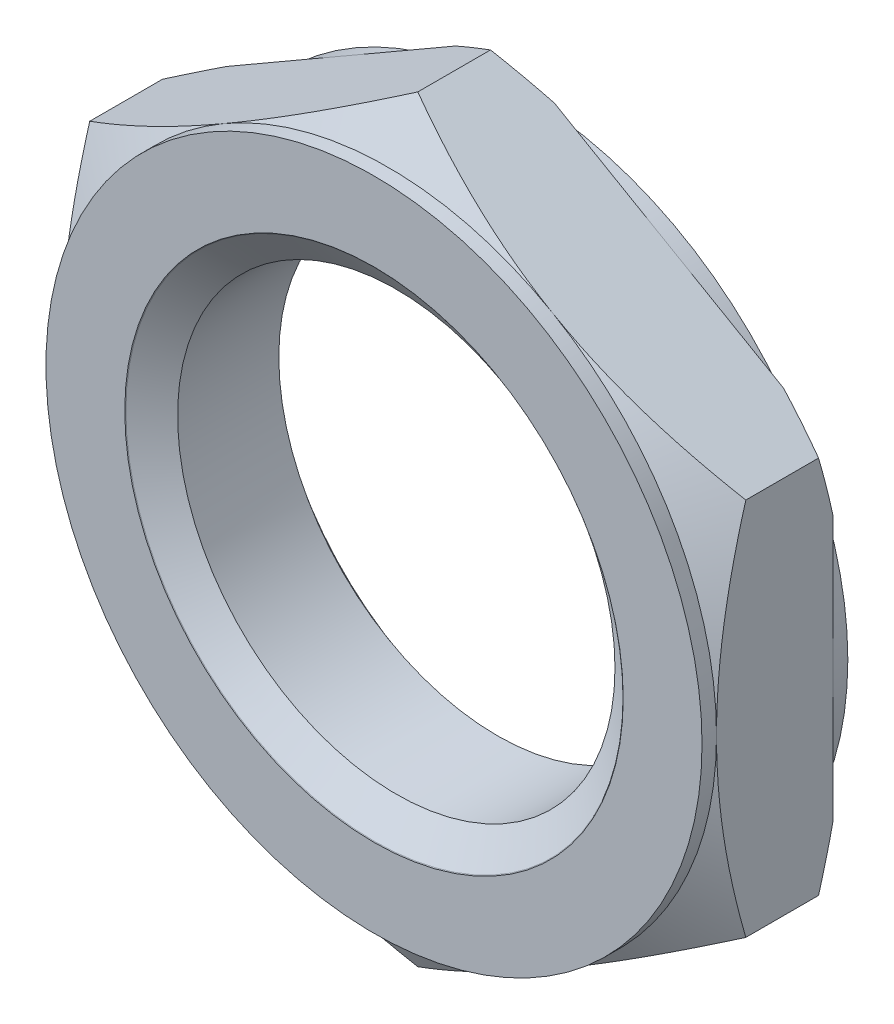
SolidWorks part; units mm, degrees
ref_plane "Plane1" through (0, 0, 0) normal (0, 0, 1) x (1, 0, 0)
ref_plane "Plane2" through (0, 0, 0) normal (0, 1, 0) x (1, 0, 0)
ref_plane "Plane3" through (0, 0, 0) normal (1, 0, 0) x (0, 0, -1)
sketch "BaseNutSke" plane through (0, 0, 0) normal (0, 0, 1) x (1, 0, 0)
  line L6 (9, 5.1962) -> (9, -5.1962)
  line L7 (-9, 5.1962) -> (-9, -5.1962)
  line L8 (9, 5.1962) -> (0, 10.3923)
  line L9 (0, 10.3923) -> (-9, 5.1962)
  line L10 (-9, -5.1962) -> (0, -10.3923)
  line L11 (0, -10.3923) -> (9, -5.1962)
  circle A0 centre (0, 0) radius 5.25
  dimension "Tap_drill" = 10.5
  dimension "Width_flats" = 18
  dimension "D2" = 9
  dimension "D3" = 9
  dimension "D1" = 120
  dimension "D4" = 9
extrude "BaseNut" add sketch "BaseNutSke" against normal blind 4
cosmetic thread "ThreadCosmetic" parameters "Thread_major"=13.675
sketch "Sketch4" plane through (0, 0, 0) normal (1, 0, 0) x (0, 0, -1)
  line L0 (4, 9) -> (3.5936, 9)
  line L1 (4, 9) -> (4, 20.3923)
  line L2 (3.5936, 20.3923) -> (4, 20.3923)
  line L3 (3.5936, 20.3923) -> (3.5936, 9)
  line L4 (0, 0) -> (34.925, 0) construction
  line L6 (4, 5.1962) -> (4, 10.3923) construction
  line L7 (0, 9) -> (-10, 9)
  line L8 (0, 5.1962) -> (0, 10.3923) construction
  line L9 (0.8038, 10.3923) -> (0.8038, 20.3923)
  line L10 (0.8038, 20.3923) -> (-10, 20.3923)
  line L11 (-10, 20.3923) -> (-10, 9)
  line L12 (0, 9) -> (0.8038, 10.3923)
  line L14 (0, 5.1962) -> (0, -5.1962) construction
  line L15 (4, 10.3923) -> (0, 10.3923) construction
  dimension "D1" = 9
  dimension "D4" = 10
  dimension "D3" = 10
  dimension "D2" = 30
  dimension "Bearing_ht" = 0.4064
revolve "Bearing-Face" cut sketch "Sketch4" angle 360 about L4
sketch "Sketch3" plane through (0, 0, 0) normal (1, 0, 0) x (0, 0, -1)
  line L0 (4, 9) -> (3.1962, 10.3923)
  line L1 (3.1962, 10.3923) -> (3.1962, 20.3923)
  line L2 (3.1962, 20.3923) -> (14, 20.3923)
  line L3 (14, 20.3923) -> (14, 9)
  line L4 (14, 9) -> (4, 9)
  line L5 (4, 5.1962) -> (4, 10.3923) construction
  line L6 (3.5936, 10.3923) -> (0.8038, 10.3923) construction
  line L7 (0, 0) -> (38.6776, 0) construction
  line L8 (4, 0) -> (0, 0) construction
  line L9 (2.1987, 10.3923) -> (2.1987, 44.222) construction
  line L10 (1.2013, 20.3923) -> (-9.6026, 20.3923)
  line L11 (-9.6026, 20.3923) -> (-9.6026, 9)
  line L12 (-9.6026, 9) -> (0.3974, 9)
  line L13 (0.3974, 9) -> (1.2013, 10.3923)
  line L14 (1.2013, 10.3923) -> (1.2013, 20.3923)
  line L16 (3.5936, 10.3923) -> (0.8038, 10.3923) construction
  dimension "D1" = 9
  dimension "D4" = 10
  dimension "D3" = 10
  dimension "D2" = 30
revolve "Double-Chamfer" cut sketch "Sketch3" angle 360 about L7
sketch "Sketch5" plane through (0, 0, 0) normal (1, 0, 0) x (0, 0, -1)
  line L0 (3.9746, 6.8375) -> (2.7519, 5.0913)
  line L1 (4.0254, 6.8375) -> (3.9746, 6.8375)
  line L2 (4.0254, 6.8375) -> (4.0254, 5.0913)
  line L3 (4.0254, 5.0913) -> (2.7519, 5.0913)
  line L6 (-0.0508, 6.8375) -> (0, 6.8375)
  line L7 (0, 6.8375) -> (1.2227, 5.0913)
  line L9 (1.2227, 5.0913) -> (-0.0508, 5.0913)
  line L10 (-0.0508, 5.0913) -> (-0.0508, 6.8375)
  line L11 (25.0375, 0) -> (38.388, 0) construction
  line L12 (4, 0) -> (0, 0) construction
  dimension "D1" = 35
  dimension "D2" = 0.0508
  dimension "ChamferDepth" = 1.7463
  dimension "Offset2" = 4.0762
  dimension "ThreadMajor" = 6.8375
  dimension "Offset1" = 4.0254
revolve "EndChamfer" cut sketch "Sketch5" angle 360 about L11
sketch "ThdSchSke" plane through (0, 0, 0) normal (0, 1, 0) x (1, 0, 0)
  line L0 (-6.8375, 0.0254) -> (-5.25, 1.137)
  line L1 (-5.25, 1.137) -> (-2.625, 1.137)
  line L2 (-2.625, 1.137) -> (-2.625, -1.0862)
  line L3 (-2.625, -1.0862) -> (-5.25, -1.0862)
  line L4 (-5.25, -1.0862) -> (-6.8375, 0.0254)
  line L5 (-3.175, 3.175) -> (3.175, 3.175) construction
  line L6 (0, 3.175) -> (0, -2.9874) construction
  line L7 (0, 2.863) -> (0, 1.1116) construction
  dimension "VeeAngle" = 70
  dimension "SideAngle" = 55
  dimension "OverCut" = 5.25
  dimension "Tap_Drill" = 10.5
  dimension "Thread_major" = 13.675
  dimension "Advance" = 3.175
  dimension "D1" = 0.0254
revolve "ThreadSchematic" cut sketch "ThdSchSke" angle 360 about L6
pattern_linear "ThdSchPat" [suppressed]
sketch "Sketch6" plane through (0, 0, 0) normal (0, 0, 1) x (1, 0, 0)
  circle A1 centre (0, 0) radius 6
  dimension "D1" = 12
extrude "Cut-Extrude1" cut sketch "Sketch6" against normal blind 10
equation "\"D2@BaseNutSke\" = \"Width_flats@BaseNutSke\" / 2"
equation "\"D3@BaseNutSke\" = \"Width_flats@BaseNutSke\" / 2"
equation "\"D1@Sketch3\" = \"Width_flats@BaseNutSke\" /2"
equation "\"D1@Sketch4\" = \"D2@BaseNutSke\""
equation "\"D4@BaseNutSke\" = \"D3@BaseNutSke\""
equation "\"Thread_major@ThdSchSke\" = \"Thread_major@ThreadCosmetic\""
equation "\"Tap_Drill@ThdSchSke\" = \"Tap_drill@BaseNutSke\""
equation "\"OverCut@ThdSchSke\" = \"Tap_Drill@ThdSchSke\" * 0.5"
equation "\"Num_threads@ThdSchPat\" = int(  ( \"Thickness@BaseNut\" - 0.0508 ) / \"Advance@ThdSchSke\" + 0.999 )  + 1"
equation "\"Advance@ThdSchPat\" = ( \"Thickness@BaseNut\" - 0.0508 ) /  (\"Num_threads@ThdSchPat\" - 1) 'relax it"
equation "' \"Num_threads@ThdSchPat\" = \"Num_threads@ThdSchPat\" - sgn( \"Num_threads@ThdSchPat\" - 1) '---chamfered tips only---"
equation "\"ThreadMajor@Sketch5\" = \"Thread_major@ThreadCosmetic\" * 0.5"
equation "\"ChamferDepth@Sketch5\" = (\"Thread_major@ThreadCosmetic\" - \"Tap_drill@BaseNutSke\") * 0.55"
equation "\"Offset1@Sketch5\" = \"Thickness@BaseNut\" + 0.0254"
equation "\"Offset2@Sketch5\" = \"Offset1@Sketch5\" + 0.0508"
